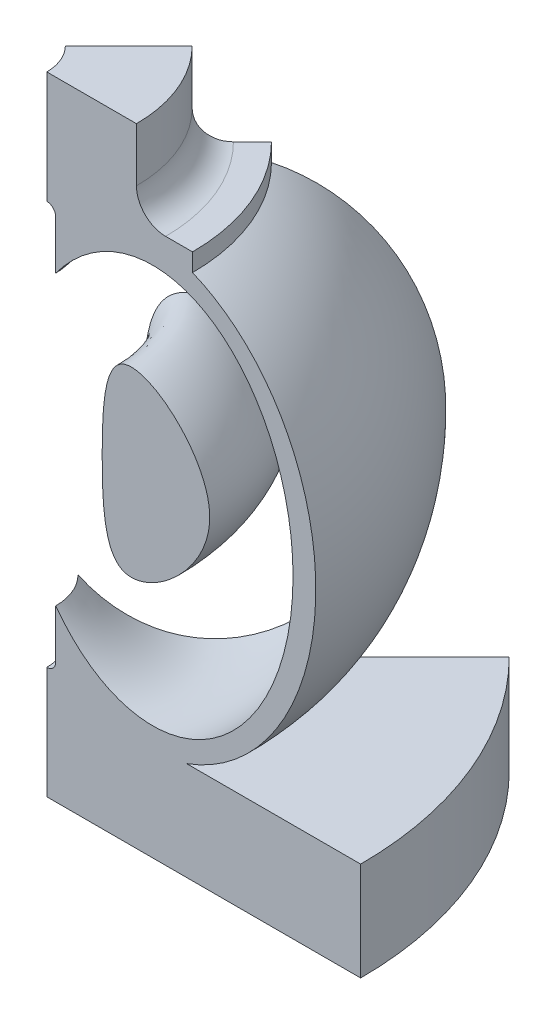
SolidWorks part; units mm, degrees
ref_plane "Plano frontal" through (0, 0, 0) normal (0, 0, 1) x (1, 0, 0)
ref_plane "Plano superior" through (0, 0, 0) normal (0, 1, 0) x (1, 0, 0)
ref_plane "Plano direito" through (0, 0, 0) normal (1, 0, 0) x (0, 0, -1)
sketch "Esboço2" plane through (0, 0, 0) normal (0, 0, 1) x (1, 0, 0)
  line L0 (0, 0) -> (0, 70000) construction
  line L1 (5000, 70000) -> (5000, 57500)
  line L2 (5000, 0) -> (5000, 12500)
  line L3 (0, 70000) -> (5000, 70000) construction
  line L4 (5000, 0) -> (0, 0) construction
  line L5 (6000, 56500) -> (6000, 13500)
  line L6 (5000, 56500) -> (5000, 57500) construction
  line L7 (5000, 13500) -> (5000, 12500) construction
  line L8 (5000, 70000) -> (15000, 70000)
  line L13 (40000, 11000) -> (40000, 0)
  line L14 (40000, 0) -> (5000, 0)
  line L15 (15000, 60000) -> (15000, 10000) construction
  line L16 (-5000, 35000) -> (35000, 35000) construction
  line L24 (40000, 11000) -> (20600, 11000)
  line L26 (15000, 70000) -> (15000, 64000)
  line L27 (18253.4927, 60746.5073) -> (21253.4927, 60746.5073)
  line L28 (21253.4927, 60746.5073) -> (21253.4927, 58746.5073)
  arc A0 (5000, 57500) -> (6000, 56500) centre (5000, 56500) cw
  arc A1 (5000, 12500) -> (6000, 13500) centre (5000, 13500) ccw
  arc A5 (15000, 64000) -> (18253.4927, 60746.5073) centre (18253.4927, 64000) ccw
  ellipse E1 centre (15000, 35000) end of major axis (15000, 60000) minor radius 20000 (20600, 11000) -> (21253.4927, 58746.5073) ccw
  point P2 (26422.5516, 11000)
  point P14 (6000, 35000)
  point P43 (0, 0)
  point P60 (0, 0)
  dimension "D12" = 45000
  dimension "D1" = 40000
  dimension "D2" = 11000
  dimension "D3" = 50000
  dimension "D4" = 40000
  dimension "D5" = 5000
  dimension "D10" = 15000
  dimension "D11" = 1000
  dimension "D20" = 10000
  dimension "D21" = 6000
  dimension "D22" = 2000
  dimension "D23" = 3000
  dimension "D24" = 70000
  dimension "D25" = 10000
revolve "Revolução2" add sketch "Esboço2" angle 45 about L0
sketch "Esboço3" plane through (0, 0, 0) normal (0, 0, 1) x (1, 0, 0)
  line L0 (32461.1782, 35000) -> (1180.0719, 35000) construction
  line L1 (0, 0) -> (0, 70000) construction
  line L2 (16820.625, 57243.3203) -> (16820.625, 12756.6797) construction
  line L3 (0, 70000) -> (5000, 70000) construction
  line L4 (35000, 35000) -> (32461.1782, 35000) construction
  line L5 (35000, 35000) -> (35000, 11000) construction
  line L6 (40000, 11000) -> (20600, 11000) construction
  ellipse E0 centre (16820.625, 35000) end of major axis (16820.625, 12756.6797) minor radius 15640.5531
  ellipse E1 centre (15000, 35000) end of major axis (15000, 60000) minor radius 20000 (20600, 11000) -> (21253.4927, 58746.5073) ccw construction
  point P1 (30445.2847, 35000)
  point P11 (16820.625, 12756.6797)
  point P28 (32461.1782, 35000)
revolve "Corte-Revolução1" cut sketch "Esboço3" angle 360 about L1
sketch "Esboço4" plane through (0, 0, 0) normal (0, 0, 1) x (1, 0, 0)
  line L0 (0, 0) -> (0, 70000) construction
  line L1 (0, 70000) -> (5000, 70000) construction
  line L2 (11179.9002, 36060.085) -> (23173.512, 36060.085) construction
  line L3 (11179.9002, 36060.085) -> (0, 36060.085) construction
  line L4 (13556.8028, 26060.085) -> (13556.8028, 46060.085) construction
  line L5 (13556.8028, 46060.085) -> (13556.8028, 26060.085) construction
  spline S0 degree 3 poles (11598.59, 20757.9608) (11001.717, 36060.085) (11598.59, 51362.2092) (29822.4546, 36060.085) (11598.59, 20757.9608) (11001.717, 36060.085) (11598.59, 51362.2092) knots -0.787213 -0.5 -0.212787 0 0.212787 0.5 0.787213 1 1.212787 1.5 1.787213 only from (11179.9002, 36060.085) to (11179.9002, 36060.085)
  point P11 (13556.8028, 36060.085)
  dimension "D1" = 11179.9002
  dimension "D2" = 20000
revolve "Revolução3" add sketch "Esboço4" angle 45 about L0
sketch "Esboço1" plane through (0, 0, 0) normal (0, 0, 1) x (1, 0, 0)
  line L0 (0, 0) -> (0, 70000) construction
  line L1 (5000, 70000) -> (5000, 57500)
  line L2 (5000, 0) -> (5000, 12500)
  line L3 (0, 70000) -> (5000, 70000) construction
  line L4 (5000, 0) -> (0, 0) construction
  line L5 (6000, 56500) -> (6000, 13500)
  line L6 (5000, 56500) -> (5000, 57500) construction
  line L7 (5000, 13500) -> (5000, 12500) construction
  line L8 (5000, 70000) -> (15000, 70000)
  line L13 (40000, 11000) -> (40000, 0)
  line L14 (40000, 0) -> (5000, 0)
  line L15 (15000, 60000) -> (15000, 10000) construction
  line L16 (-5000, 35000) -> (35000, 35000) construction
  line L17 (30768.985, 51308.0387) -> (31190.1207, 51577.5656)
  line L18 (31190.1207, 51577.5656) -> (31729.1744, 50735.2942)
  line L19 (31729.1744, 50735.2942) -> (31308.0387, 50465.7673)
  line L20 (30768.985, 51308.0387) -> (31308.0387, 50465.7673) construction
  line L21 (31459.6476, 51156.4299) -> (30617.3762, 50617.3762) construction
  line L22 (30617.3762, 50617.3762) -> (30886.903, 50196.2405) construction
  line L23 (30617.3762, 50617.3762) -> (15000, 35000) construction
  line L24 (40000, 11000) -> (20600, 11000)
  line L25 (30886.903, 50196.2405) -> (31308.0387, 50465.7673) construction
  line L26 (15000, 70000) -> (15000, 64000)
  line L27 (18253.4927, 60746.5073) -> (21253.4927, 60746.5073)
  line L28 (21253.4927, 60746.5073) -> (21253.4927, 58746.5073)
  line L29 (15000, 35000) -> (30617.3762, 19382.6238) construction
  line L30 (30617.3762, 19382.6238) -> (30886.903, 19803.7595) construction
  line L31 (31308.3371, 19534.0417) -> (31728.8763, 19264.8966)
  line L32 (31728.8763, 19264.8966) -> (31189.8226, 18422.6252)
  line L33 (31189.8226, 18422.6252) -> (30768.6869, 18692.152)
  line L34 (31459.3495, 18843.7609) -> (30617.3762, 19382.6238) construction
  line L35 (31308.3371, 19534.0417) -> (30886.903, 19803.7595) construction
  line L36 (36200, 37500) -> (36200, 38000)
  line L37 (36200, 38000) -> (37700, 38000)
  line L38 (37700, 38000) -> (37700, 37500)
  line L39 (36200, 32500) -> (36200, 32000)
  line L40 (36200, 32000) -> (37700, 32000)
  line L41 (37700, 32000) -> (37700, 32500)
  line L42 (35000, 35000) -> (35700, 35000) construction
  line L46 (37700, 37500) -> (38200, 37500)
  line L47 (38200, 37500) -> (38200, 32500)
  line L48 (38200, 32500) -> (37700, 32500)
  line L49 (35700, 37500) -> (36200, 37500)
  line L50 (35700, 37500) -> (35700, 32500) construction
  line L51 (35700, 32500) -> (36200, 32500)
  arc A0 (5000, 57500) -> (6000, 56500) centre (5000, 56500) cw
  arc A1 (5000, 12500) -> (6000, 13500) centre (5000, 13500) ccw
  arc A3 (30768.985, 51308.0387) -> (30061.5405, 51448.3091) centre (30488.3116, 51746.591) cw
  arc A4 (31308.0387, 50465.7673) -> (31139.5014, 49764.6376) centre (31588.5135, 50027.5256) ccw
  arc A5 (15000, 64000) -> (18253.4927, 60746.5073) centre (18253.4927, 64000) ccw
  arc A6 (30061.739, 18551.9749) -> (30768.6869, 18692.152) centre (30488.2122, 18253.9103) cw
  arc A7 (31139.6768, 20235.662) -> (31308.3371, 19534.0417) centre (31589.0106, 19972.5939) ccw
  arc A8 (34826.5097, 38285.744) -> (35700, 37500) centre (35700, 38378.3897) ccw
  arc A9 (35700, 32500) -> (34826.5097, 31714.256) centre (35700, 31621.6103) ccw
  ellipse E1 centre (15000, 35000) end of major axis (15000, 60000) minor radius 20000 (15000, 10000) -> (21253.4927, 58746.5073) ccw
  point P14 (6000, 35000)
  dimension "D12" = 45000
  dimension "D1" = 40000
  dimension "D2" = 11000
  dimension "D3" = 50000
  dimension "D4" = 40000
  dimension "D5" = 5000
  dimension "D6" = 45
  dimension "D7" = 1000
  dimension "D8" = 500
  dimension "D9" = 1000
  dimension "D10" = 15000
  dimension "D11" = 1000
  dimension "D13" = 45
  dimension "D14" = 500
  dimension "D15" = 1500
  dimension "D16" = 500
  dimension "D17" = 5000
  dimension "D18" = 500
  dimension "D19" = 700
  dimension "D20" = 10000
  dimension "D21" = 6000
  dimension "D22" = 2000
  dimension "D23" = 3000
  dimension "D24" = 70000
  dimension "D25" = 10000
